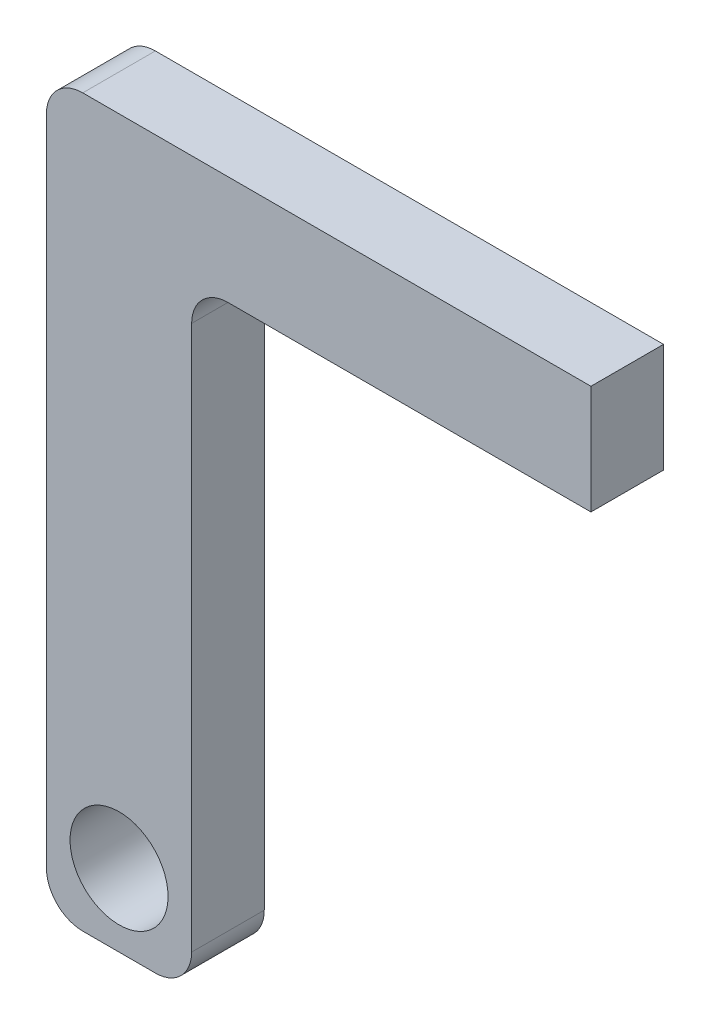
SolidWorks part; units mm, degrees
ref_plane "Ön Düzlem" through (0, 0, 0) normal (0, 0, 1) x (1, 0, 0)
ref_plane "Üst Düzlem" through (0, 0, 0) normal (0, 1, 0) x (1, 0, 0)
ref_plane "Sağ Düzlem" through (0, 0, 0) normal (1, 0, 0) x (0, 0, -1)
sketch "Sketch1" plane through (0, 0, 0) normal (0, 0, 1) x (1, 0, 0)
  line L1 (-20, 85) -> (20, 85)
  line L2 (-20, 85) -> (-20, -85)
  line L3 (-20, -85) -> (20, -85)
  line L4 (20, 85) -> (20, -85)
  line L5 (-20, 85) -> (20, -85) construction
  line L6 (-20, -85) -> (20, 85) construction
  point P0 (0, 0)
  dimension "D1" = 40
  dimension "D2" = 170
extrude "Boss-Extrude1" add sketch "Sketch1" along normal blind 20
sketch "Sketch2" plane through (0, 85, 0) normal (0, 1, 0) x (1, 0, 0)
  line L1 (-20, 0) -> (130, 0)
  line L2 (-20, 0) -> (-20, -20)
  line L3 (-20, -20) -> (130, -20)
  line L4 (130, 0) -> (130, -20)
  dimension "D1" = 20
  dimension "D2" = 150
extrude "Boss-Extrude2" add sketch "Sketch2" along normal blind 30
fillet "Fillet1" radius 10 3 edges at (20, -85, 10) (-20, -85, 10) (-20, 115, 10)
sketch "Sketch3" plane through (0, 0, 20) normal (0, 0, 1) x (1, 0, 0)
  line L0 (-10, -85) -> (10, -85) construction
  line L1 (-20, 105) -> (-20, -75) construction
  circle A0 centre (0, -65) radius 13.5
  dimension "D1" = 20
  dimension "D2" = 20
extrude "Cut-Extrude1" cut sketch "Sketch3" against normal up to next
fillet "Fillet2" radius 10 1 edges
